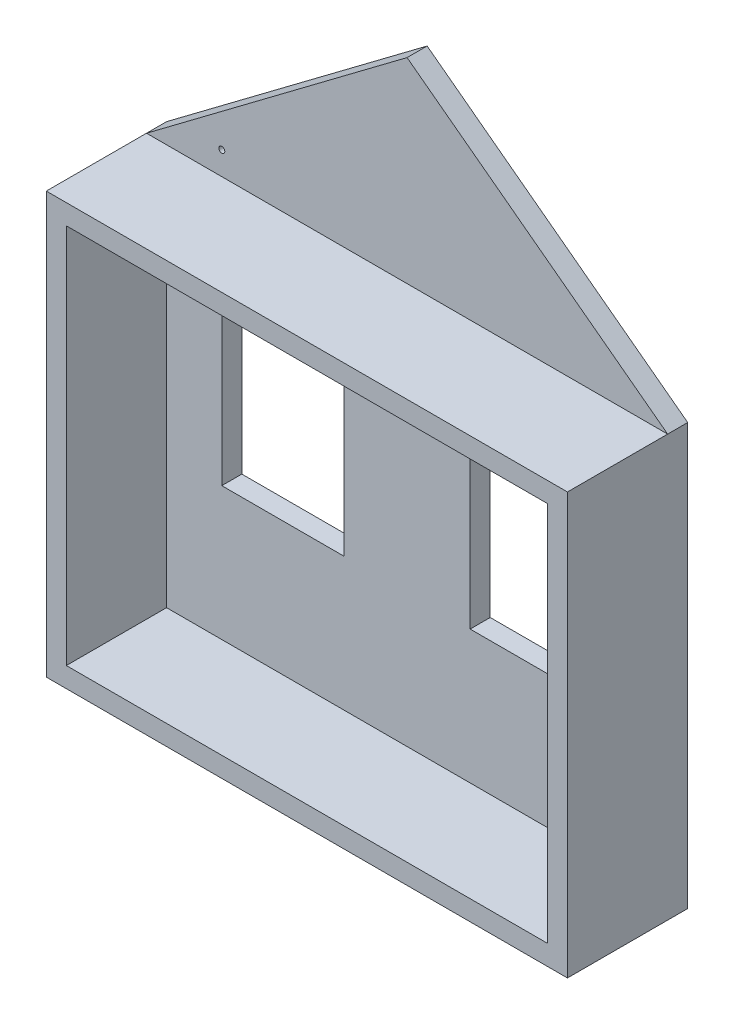
SolidWorks part; units mm, degrees
ref_plane "Спереди" through (0, 0, 0) normal (0, 0, 1) x (1, 0, 0)
ref_plane "Сверху" through (0, 0, 0) normal (0, 1, 0) x (1, 0, 0)
ref_plane "Справа" through (0, 0, 0) normal (1, 0, 0) x (0, 0, -1)
sketch "Эскиз2" plane through (0, 0, 0) normal (0, 0, 1) x (1, 0, 0)
  line L1 (0, 0) -> (2500, 0)
  line L2 (0, 0) -> (0, 2000)
  line L3 (0, 2000) -> (2500, 2000)
  line L4 (2500, 0) -> (2500, 2000)
extrude "Вытянуть-Тонкостенный1" add sketch "Эскиз2" along normal blind 500 thin thin type mid plane wall 100
sketch "Эскиз3" plane through (0, 0, 0) normal (0, 0, -1) x (-1, 0, 0)
  line L0 (-1250, 3026.7858) -> (-1250, -50) construction
  line L2 (-2550, 2050) -> (-2550, -50)
  line L3 (-2550, -50) -> (50, -50)
  line L4 (50, 2050) -> (50, -50)
  line L9 (-935.3169, 1631.5845) -> (-325.5344, 1631.5845)
  line L10 (-935.3169, 1631.5845) -> (-935.3169, 714.9564)
  line L11 (-935.3169, 714.9564) -> (-325.5344, 714.9564)
  line L12 (-325.5344, 1631.5845) -> (-325.5344, 714.9564)
  line L13 (-2174.4656, 1631.5845) -> (-2174.4656, 714.9564)
  line L14 (-1564.6831, 714.9564) -> (-2174.4656, 714.9564)
  line L15 (-1564.6831, 1631.5845) -> (-1564.6831, 714.9564)
  line L16 (-1564.6831, 1631.5845) -> (-2174.4656, 1631.5845)
  line L19 (50, -50) -> (-2550, -50) construction
  line L20 (50, 2050) -> (-1250, 3026.7858)
  line L21 (-1250, 3026.7858) -> (-2550, 2050)
  circle A0 centre (-325.5344, 2166.1664) radius 15
extrude "Бобышка-Вытянуть1" add sketch "Эскиз3" along normal blind 100
sketch "Эскиз4" plane through (0, 0, -100) normal (0, 0, -1) x (-1, 0, 0)
  line L0 (-2379.0003, 2086.7757) -> (-1259.9587, 2935.6368)
  line L1 (-1259.9587, 2935.6368) -> (-89.2076, 2086.7757)
  line L2 (-89.2076, 2086.7757) -> (-2379.0003, 2086.7757)
extrude "Вырез-Вытянуть1" cut sketch "Эскиз4" against normal blind 70
